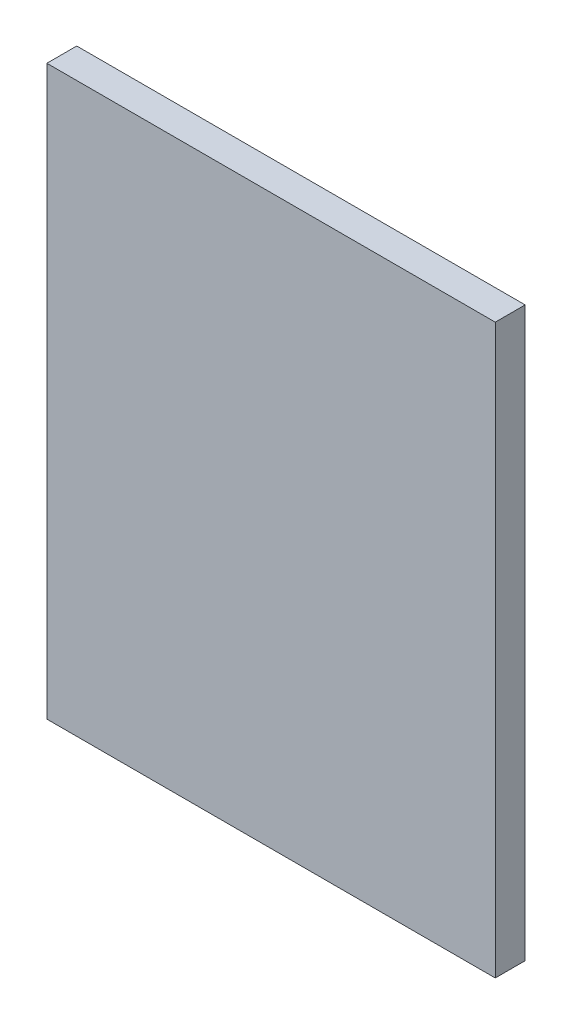
SolidWorks part; units mm, degrees
ref_plane "Front Plane" through (0, 0, 0) normal (0, 0, 1) x (1, 0, 0)
ref_plane "Top Plane" through (0, 0, 0) normal (0, 1, 0) x (1, 0, 0)
ref_plane "Right Plane" through (0, 0, 0) normal (1, 0, 0) x (0, 0, -1)
sketch "Sketch1" plane through (0, 0, 0) normal (0, 0, 1) x (1, 0, 0)
  line L1 (0, 0) -> (75, 0)
  line L2 (0, 0) -> (0, 95)
  line L3 (0, 95) -> (75, 95)
  line L4 (75, 0) -> (75, 95)
  dimension "D1" = 75
  dimension "D2" = 95
extrude "Boss-Extrude1" add sketch "Sketch1" along normal blind 5
